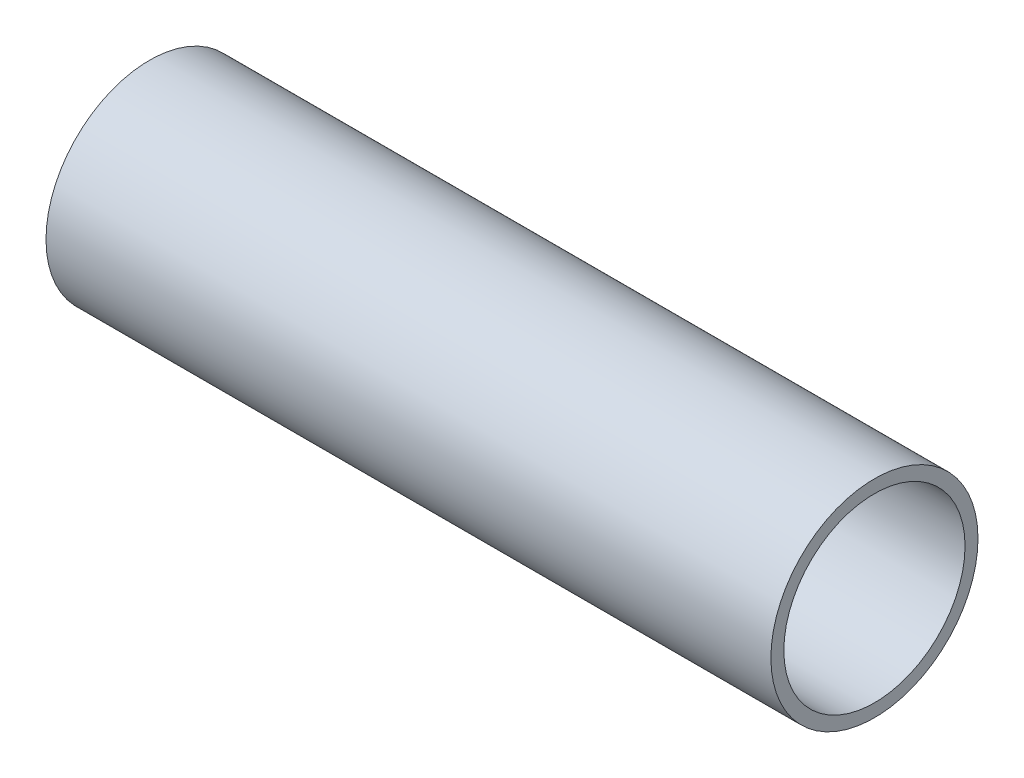
SolidWorks part; units mm, degrees
material "6061-T6 (SS)"
ref_plane "Front Plane" through (0, 0, 0) normal (0, 0, 1) x (1, 0, 0)
ref_plane "Top Plane" through (0, 0, 0) normal (0, 1, 0) x (1, 0, 0)
ref_plane "Right Plane" through (0, 0, 0) normal (1, 0, 0) x (0, 0, -1)
sketch "Sketch1" plane through (0, 0, 0) normal (1, 0, 0) x (0, 0, -1)
  circle A0 centre (0, 0) radius 25.4
  circle A1 centre (0, 0) radius 22.225
  dimension "D1" = 50.8
  dimension "D2" = 3.175
extrude "Boss-Extrude1" add sketch "Sketch1" along normal blind 177.8
